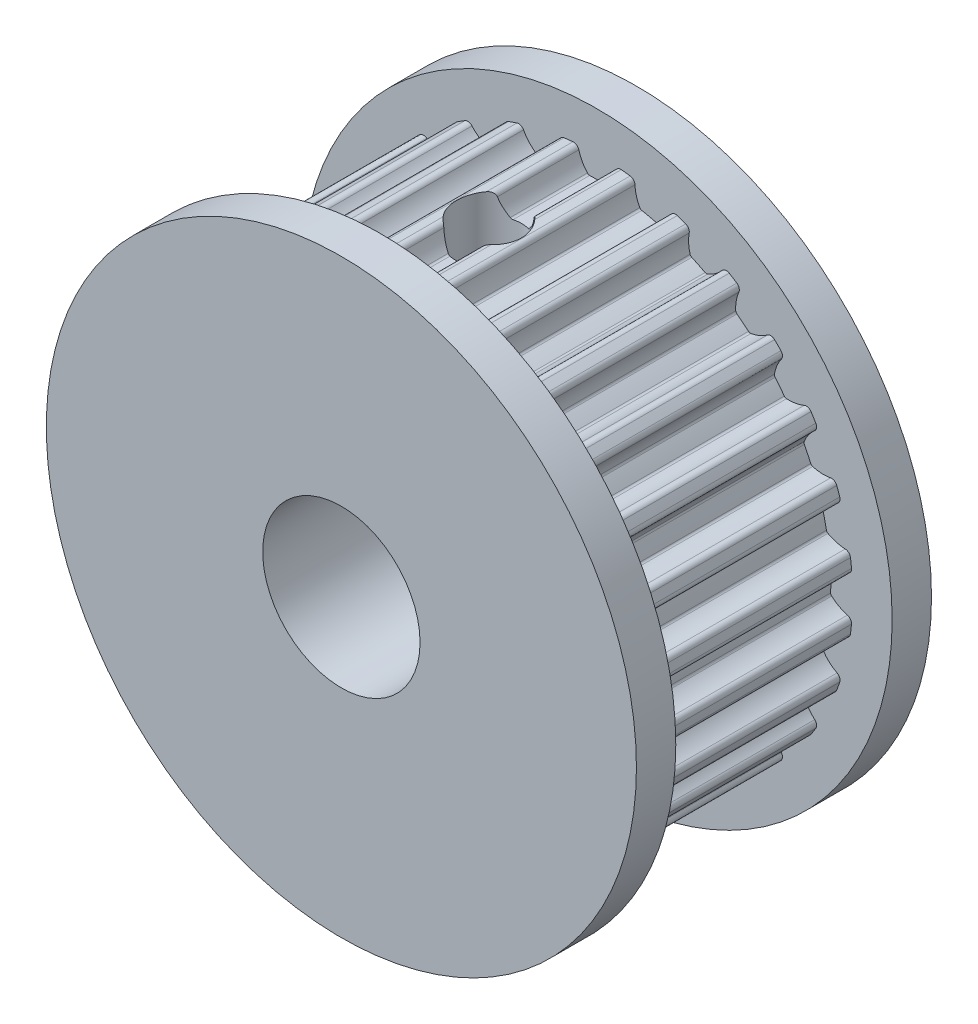
SolidWorks part; units mm, degrees
material "6061-T6 (SS)"
ref_plane "前基準面" through (0, 0, 0) normal (0, 0, 1) x (1, 0, 0)
ref_plane "上基準面" through (0, 0, 0) normal (0, 1, 0) x (1, 0, 0)
ref_plane "右基準面" through (0, 0, 0) normal (1, 0, 0) x (0, 0, -1)
sketch "草圖1" plane through (0, 0, 0) normal (0, 0, 1) x (1, 0, 0)
  circle A0 centre (0, 0) radius 12.99
  dimension "D1" = 25.98
extrude "填料-伸長1" add sketch "草圖1" along normal mid plane 11
sketch "草圖2" plane through (0, 0, 5.5) normal (0, 0, 1) x (1, 0, 0)
  line L0 (0, 0) -> (0, 13.244) construction
  line L1 (-0.975, 13.244) -> (0.975, 13.244) construction
  arc A0 (-0.3775, 11.874) -> (0.3775, 11.874) centre (0, 0) cw
  circle A1 centre (0, 0) radius 12.99 construction
  arc A2 (-1.2277, 12.9319) -> (-0.931, 12.7265) centre (-1.2012, 12.6531) cw
  arc A3 (-0.931, 12.7265) -> (-0.4938, 11.9236) centre (0.975, 13.244) ccw
  arc A4 (-0.4938, 11.9236) -> (-0.3775, 11.874) centre (-0.3822, 12.0239) ccw
  arc A5 (0.4938, 11.9236) -> (0.3775, 11.874) centre (0.3822, 12.0239) cw
  arc A6 (0.931, 12.7265) -> (0.4938, 11.9236) centre (-0.975, 13.244) cw
  arc A7 (1.2277, 12.9319) -> (0.931, 12.7265) centre (1.2012, 12.6531) ccw
  point P6 (0, 11.88)
  point P18 (0, 12.99)
  dimension "D1" = 1.11
  dimension "D2" = 0.15
  dimension "D3" = 1.975
  dimension "D4" = 0.28
  dimension "D5" = 1.95
  dimension "D6" = 0.254
extrude "除料-伸長1" cut sketch "草圖2" against normal through all and the other way through all flip side to cut
pattern_circular "環狀複製排列1" count 28 over 360 about axis through (0, 0, 5.5) along (0, 0, 1) of "除料-伸長1"
sketch "草圖3" plane through (0, 0, 5.5) normal (0, 0, 1) x (1, 0, 0)
  circle A0 centre (0, 0) radius 15
  dimension "D1" = 30
extrude "填料-伸長2" add sketch "草圖3" along normal blind 2
mirror "鏡射1" about plane through (0, 0, 0) normal (0, 0, 1) of "填料-伸長2"
sketch "草圖4" plane through (0, 0, 7.5) normal (0, 0, 1) x (1, 0, 0)
  circle A0 centre (0, 0) radius 4
  dimension "D1" = 8
extrude "除料-伸長2" cut sketch "草圖4" against normal through all
hole_wizard "M4x0.7 螺紋孔1" positions "草圖5" profile "草圖6" tap size "M4x0.7" standard "Ansi Metric"
sketch "草圖5" plane through (0, 0, 0) normal (0, 1, 0) x (1, 0, 0)
  point P0 (0, 0)
sketch "草圖6" plane through (0, 0, 0) normal (1, 0, 0) x (0, 0, -1)
  line L0 (0, 0) -> (0, 15)
  line L1 (0, 15) -> (1.65, 15)
  line L2 (1.65, 15) -> (1.65, 0)
  line L5 (1.65, 0) -> (0, 0)
  line L11 (0, -6.35) -> (0, 107.95) construction
  dimension "貫穿螺孔鑽直徑" = 3.3
  dimension "貫穿螺孔鑽深度" = 15
pattern_circular "環狀複製排列2" count 2 every 90 about axis through (0, 0, 7.5) along (0, 0, 1) of "M4x0.7 螺紋孔1"
